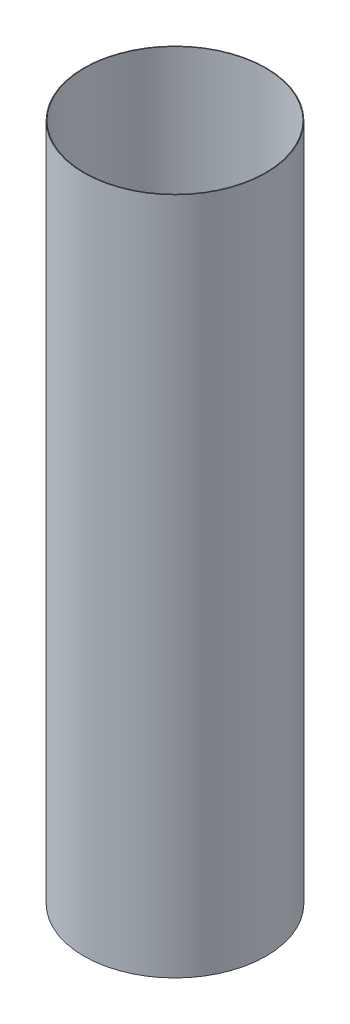
SolidWorks part; units mm, degrees
material "Hexcel AS4C (3000 Filaments)"
ref_plane "Front Plane" through (0, 0, 0) normal (0, 0, 1) x (1, 0, 0)
ref_plane "Top Plane" through (0, 0, 0) normal (0, 1, 0) x (1, 0, 0)
ref_plane "Right Plane" through (0, 0, 0) normal (1, 0, 0) x (0, 0, -1)
sketch "Sketch1" plane through (0, 0, 0) normal (0, 1, 0) x (1, 0, 0)
  circle A0 centre (0, 0) radius 76.2 construction
  circle A1 centre (0, 0) radius 76.708
  circle A2 centre (0, 0) radius 77.216
  dimension "D1" = 152.4
  dimension "D2" = 0.508
  dimension "D3" = 0.508
extrude "Boss-Extrude1" add sketch "Sketch1" along normal blind 574.7085
equation "\"nominalLength\"= 24in"
equation "\"interfaceOffset\"= 0.68684in"
equation "\"sheetLength\"= \"nominalLength\" - 2 * \"interfaceOffset\""
equation "\"D1@Boss-Extrude1\"=\"sheetLength\""
